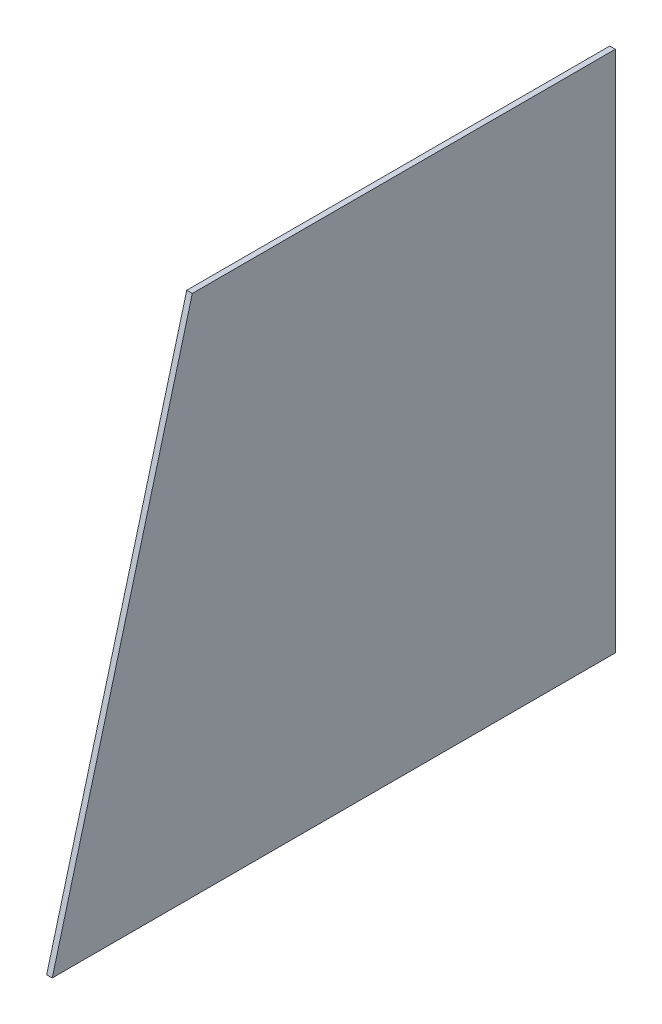
SolidWorks part; units mm, degrees
ref_plane "Front Plane" through (0, 0, 0) normal (0, 0, 1) x (1, 0, 0)
ref_plane "Top Plane" through (0, 0, 0) normal (0, 1, 0) x (1, 0, 0)
ref_plane "Right Plane" through (0, 0, 0) normal (1, 0, 0) x (0, 0, -1)
sketch "Sketch1" plane through (0, 0, 0) normal (1, 0, 0) x (0, 0, -1)
  line L0 (-76.2744, 140.9304) -> (151.7988, 140.9304)
  line L1 (151.7988, 140.9304) -> (151.7988, -140.9304)
  line L2 (-151.7988, -140.9304) -> (151.7988, -140.9304)
  line L3 (-151.7988, -140.9304) -> (-76.2744, 140.9304)
extrude "Boss-Extrude1" add sketch "Sketch1" along normal blind 3
